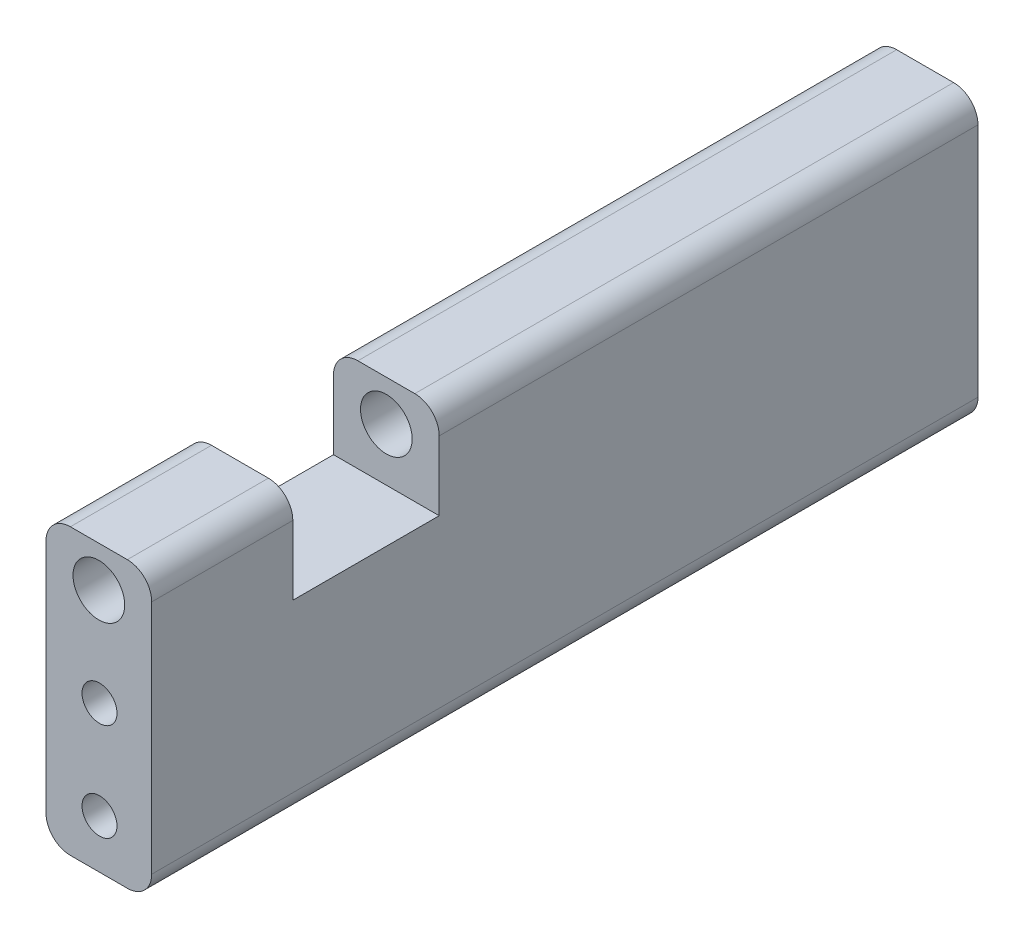
SolidWorks part; units mm, degrees
ref_plane "Front Plane" through (0, 0, 0) normal (0, 0, 1) x (1, 0, 0)
ref_plane "Top Plane" through (0, 0, 0) normal (0, 1, 0) x (1, 0, 0)
ref_plane "Right Plane" through (0, 0, 0) normal (1, 0, 0) x (0, 0, -1)
sketch "Sketch1" plane through (0, 0, 0) normal (0, 0, 1) x (1, 0, 0)
  line L0 (6.5, 0) -> (6.5, 35) construction
  line L5 (0, 0) -> (13, 0)
  line L6 (0, 0) -> (0, 35)
  line L7 (0, 35) -> (13, 35)
  line L8 (13, 0) -> (13, 35)
  circle A0 centre (6.5, 30) radius 3.175
  dimension "D2" = 6.35
  dimension "D1" = 5
  dimension "D3" = 13
  dimension "D4" = 35
extrude "Boss-Extrude1" add sketch "Sketch1" along normal blind 101.6
ref_plane "Plane1" through (0, 0, 75.25) normal (0, 0, 1) x (1, 0, 0)
sketch "Sketch2" plane through (0, 0, 75.25) normal (0, 0, 1) x (1, 0, 0)
  line L0 (0, 35) -> (0, 0) construction
  line L1 (0, 30) -> (0, 35)
  line L2 (0, 35) -> (13, 35)
  line L3 (13, 35) -> (13, 30)
  line L4 (0, 30) -> (0, 23.5)
  line L5 (0, 23.5) -> (13, 23.5)
  line L6 (13, 0) -> (13, 35) construction
  line L7 (13, 23.5) -> (13, 30)
  arc A0 (0, 30) -> (13, 30) centre (6.5, 30) ccw construction
extrude "Cut-Extrude1" cut sketch "Sketch2" against normal mid plane 18
hole_wizard "M4 Clearance Hole1" positions "Sketch3" profile "Sketch6" hole size "M4" standard "ANSI Metric"
sketch "Sketch3" plane through (0, 0, 0) normal (0, 0, -1) x (-1, 0, 0)
  line L0 (0, 0) -> (-13, 0) construction
  point P0 (-6.5792, 18)
  point P2 (-6.5792, 6)
  dimension "D1" = 6
  dimension "D2" = 12
sketch "Sketch6" plane through (6.5792, 18, 0) normal (1, 0, 0) x (0, 1, 0)
  line L0 (0, 0) -> (0, 6.2919)
  line L1 (0, 6.2919) -> (2.15, 5)
  line L2 (2.15, 5) -> (2.15, 0)
  line L5 (2.15, 0) -> (0, 0)
  line L10 (0, 6.2919) -> (-2.15, 5) construction
  line L11 (0, -6.35) -> (0, 107.95) construction
  dimension "Hole Dia." = 4.3
  dimension "Hole Depth" = 5
  dimension "Drill Angle" = 118
hole_wizard "M4 Clearance Hole2" positions "Sketch7" profile "Sketch8" hole size "M4" standard "ANSI Metric"
sketch "Sketch7" plane through (0, 0, 101.6) normal (0, 0, 1) x (1, 0, 0)
  point P0 (6.5792, 18)
  point P3 (6.5792, 6)
sketch "Sketch8" plane through (6.5792, 18, 101.6) normal (1, 0, 0) x (0, -1, 0)
  line L0 (0, 0) -> (0, 6.2919)
  line L1 (0, 6.2919) -> (2.15, 5)
  line L2 (2.15, 5) -> (2.15, 0)
  line L5 (2.15, 0) -> (0, 0)
  line L10 (0, 6.2919) -> (-2.15, 5) construction
  line L11 (0, -6.35) -> (0, 107.95) construction
  dimension "Hole Dia." = 4.3
  dimension "Hole Depth" = 5
  dimension "Drill Angle" = 118
fillet "Fillet1" radius 3 6 edges at (0, 0, 50.8) (13, 0, 50.8) (0, 35, 92.925) (13, 35, 92.925) (0, 35, 33.125) (13, 35, 33.125)
